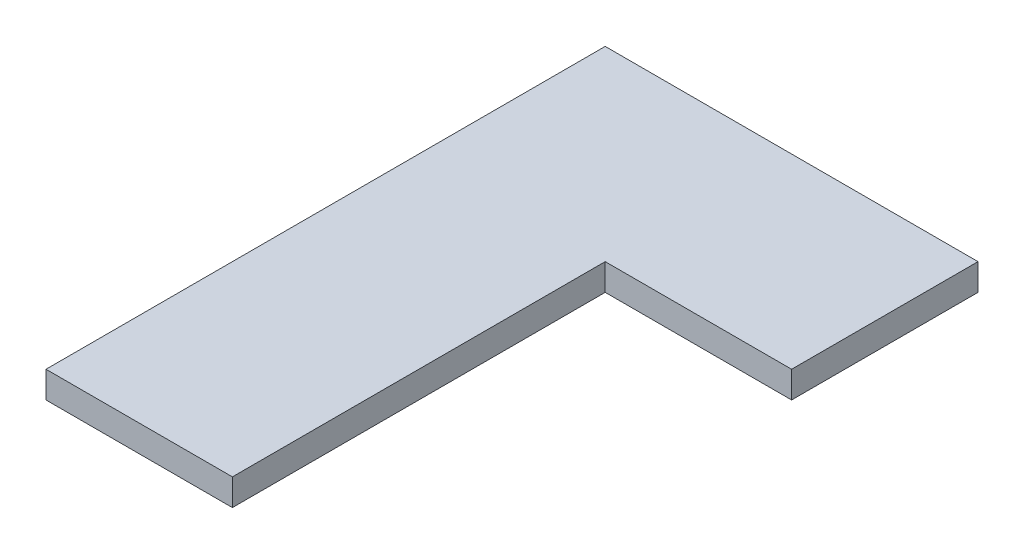
SolidWorks part; units mm, degrees
ref_plane "Front Plane" through (0, 0, 0) normal (0, 0, 1) x (1, 0, 0)
ref_plane "Top Plane" through (0, 0, 0) normal (0, 1, 0) x (1, 0, 0)
ref_plane "Right Plane" through (0, 0, 0) normal (1, 0, 0) x (0, 0, -1)
sketch "Sketch1" plane through (0, 0, 0) normal (0, 1, 0) x (1, 0, 0)
  line L0 (-70, 105) -> (70, -105) construction
  line L1 (-70, 105) -> (70, 105) construction
  line L2 (-70, 105) -> (-70, -105) construction
  line L3 (-70, -105) -> (70, -105) construction
  line L4 (70, 105) -> (70, -105) construction
  line L5 (0, -105) -> (0, 35)
  line L6 (0, 35) -> (70, 35)
  line L7 (70, 105) -> (70, 35)
  line L8 (70, 105) -> (-70, 105)
  line L9 (-70, 105) -> (-70, -105)
  line L10 (-70, -105) -> (0, -105)
  dimension "D1" = 140
  dimension "D2" = 210
  dimension "D3" = 70
extrude "Boss-Extrude1" add sketch "Sketch1" along normal blind 10
